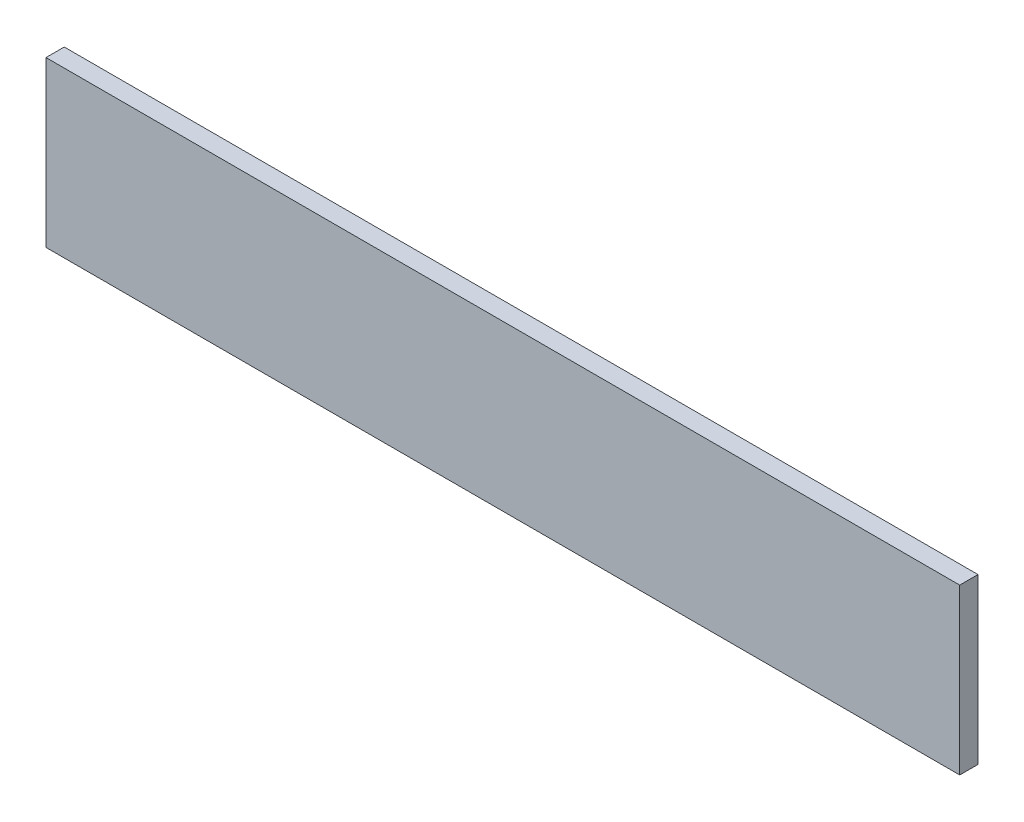
SolidWorks part; units mm, degrees
ref_plane "Front Plane" through (0, 0, 0) normal (0, 0, 1) x (1, 0, 0)
ref_plane "Top Plane" through (0, 0, 0) normal (0, 1, 0) x (1, 0, 0)
ref_plane "Right Plane" through (0, 0, 0) normal (1, 0, 0) x (0, 0, -1)
sketch "Sketch1" plane through (0, 0, 0) normal (0, 0, 1) x (1, 0, 0)
  line L1 (-317.5, -57.15) -> (317.5, -57.15)
  line L2 (-317.5, -57.15) -> (-317.5, 57.15)
  line L3 (-317.5, 57.15) -> (317.5, 57.15)
  line L4 (317.5, -57.15) -> (317.5, 57.15)
  line L5 (-317.5, -57.15) -> (317.5, 57.15) construction
  line L6 (-317.5, 57.15) -> (317.5, -57.15) construction
  point P0 (0, 0)
  dimension "D1" = 114.3
  dimension "D2" = 635
extrude "Boss-Extrude1" add sketch "Sketch1" along normal blind 12.7
